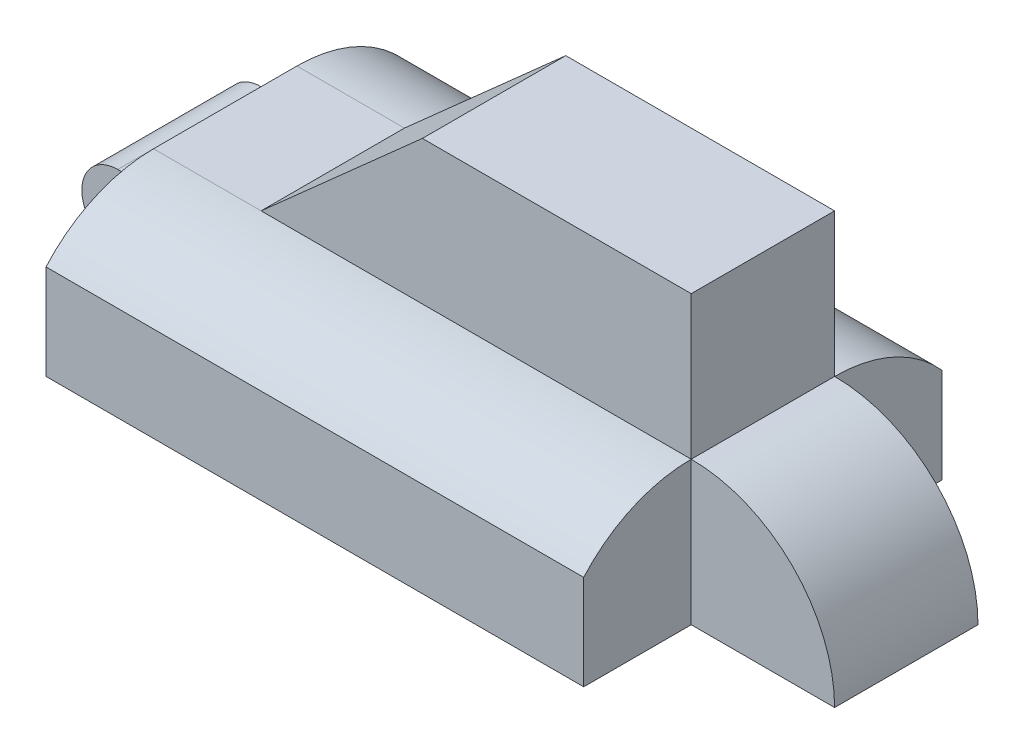
SolidWorks part; units mm, degrees
ref_plane "Front Plane" through (0, 0, 0) normal (0, 0, 1) x (1, 0, 0)
ref_plane "Top Plane" through (0, 0, 0) normal (0, 1, 0) x (1, 0, 0)
ref_plane "Right Plane" through (0, 0, 0) normal (1, 0, 0) x (0, 0, -1)
sketch "Sketch1" plane through (0, 0, 0) normal (0, 1, 0) x (1, 0, 0)
  line L1 (47.625, 31.75) -> (-47.625, 31.75)
  line L2 (47.625, 31.75) -> (47.625, -31.75)
  line L3 (47.625, -31.75) -> (-47.625, -31.75)
  line L4 (-47.625, 31.75) -> (-47.625, -31.75)
  line L5 (47.625, 31.75) -> (-47.625, -31.75) construction
  line L6 (47.625, -31.75) -> (-47.625, 31.75) construction
  point P0 (0, 0)
extrude "Boss-Extrude1" add sketch "Sketch1" along normal blind 25.4 contours L2 L3 L4 L1
sketch "Sketch2" plane through (0, 25.4, 0) normal (0, 1, 0) x (1, 0, 0)
  line L0 (47.625, 31.75) -> (-47.625, 31.75) construction
  line L1 (47.625, -12.7) -> (-28.575, -12.7)
  line L2 (47.625, -12.7) -> (47.625, 12.7)
  line L3 (47.625, 12.7) -> (-28.575, 12.7)
  line L4 (-28.575, -12.7) -> (-28.575, 12.7)
  line L5 (47.625, -12.7) -> (-28.575, 12.7) construction
  line L6 (47.625, 12.7) -> (-28.575, -12.7) construction
  line L7 (47.625, 31.75) -> (47.625, -31.75) construction
  point P0 (9.525, 0)
  dimension "D1" = 31.75
  dimension "D2" = 25.4
  dimension "D3" = 76.2
  dimension "D4" = 0
extrude "Boss-Extrude2" add sketch "Sketch2" along normal blind 25.4
sketch "Sketch3" plane through (0, 0, 12.7) normal (0, 0, 1) x (1, 0, 0)
  line L0 (-28.575, 25.4) -> (0, 50.8)
  line L1 (-28.575, 50.8) -> (47.625, 50.8) construction
  line L2 (0, 50.8) -> (-28.575, 25.4)
  line L3 (-28.575, 50.8) -> (-28.575, 25.4)
  line L4 (-28.575, 50.8) -> (0, 50.8)
  line M3 (47.625, 50.8) -> (-28.575, 50.8)
  line M4 (-28.575, 50.8) -> (-28.575, 25.4)
extrude "Cut-Extrude1" cut sketch "Sketch3" against normal blind 25.4 contours L0 M4 M3
sketch "Sketch4" plane through (47.625, 0, 0) normal (1, 0, 0) x (0, 0, -1)
  line L0 (31.75, 0) -> (-31.75, 0) construction
  line L1 (-12.7, 25.4) -> (12.7, 25.4)
  line L2 (-12.7, 25.4) -> (-12.7, 0)
  line L3 (-12.7, 0) -> (12.7, 0)
  line L4 (12.7, 25.4) -> (12.7, 0)
  dimension "D1" = 25.4
extrude "Boss-Extrude3" add sketch "Sketch4" along normal blind 25.4
sketch "Sketch5" plane through (0, 0, -12.7) normal (0, 0, -1) x (-1, 0, 0)
  line L0 (-73.025, 0) -> (-73.025, 25.4) construction
  line L1 (-73.025, 0) -> (-47.625, 0)
  line L2 (-47.625, 0) -> (-47.625, 25.4)
  line L3 (-73.025, 0) -> (-73.025, 25.4)
  line L4 (-73.025, 25.4) -> (-47.625, 25.4)
  arc A0 (-47.625, 25.4) -> (-73.025, 0) centre (-47.625, 0) ccw
  line M5 (-47.625, 25.4) -> (-73.025, 25.4)
  line M6 (-73.025, 25.4) -> (-73.025, 0)
extrude "Cut-Extrude2" cut sketch "Sketch5" against normal blind 25.4 contours A0 M5 M6
sketch "Sketch7" plane through (47.625, 0, 0) normal (1, 0, 0) x (0, 0, -1)
  line L0 (-31.75, 25.4) -> (-31.75, 0) construction
  line L1 (31.75, 25.4) -> (31.75, 0) construction
  line L2 (-31.75, 16.8005) -> (-31.75, 25.4)
  line L3 (-31.75, 25.4) -> (-12.7, 25.4)
  line L4 (12.7, 25.4) -> (31.75, 25.4)
  line L5 (31.75, 25.4) -> (31.75, 16.8005)
  arc A0 (-12.7, 25.4) -> (-31.75, 16.8005) centre (-12.7, 0) ccw
  arc A1 (12.7, 25.4) -> (31.75, 16.8005) centre (12.7, 0) cw
extrude "Cut-Extrude3" cut sketch "Sketch7" against normal blind 95.25 contours L3 A0 L2 | L5 A1 L4
sketch "." plane through (-47.625, 0, 0) normal (-1, 0, 0) x (0, 0, 1)
  line L1 (12.7, 6.35) -> (-12.7, 6.35)
  line L2 (12.7, 6.35) -> (12.7, 19.05)
  line L3 (12.7, 19.05) -> (-12.7, 19.05)
  line L4 (-12.7, 6.35) -> (-12.7, 19.05)
  line L6 (-12.7, 25.4) -> (12.7, 25.4) construction
  dimension "D1" = 25.4
  dimension "D2" = 12.7
  dimension "D3" = 6.35
extrude "Boss-Extrude4" add sketch "." along normal blind 12.7
sketch "Sketch9" plane through (0, 0, 12.7) normal (0, 0, 1) x (1, 0, 0)
  line L0 (-60.325, 6.35) -> (-60.325, 19.05) construction
  line L1 (-60.325, 19.05) -> (-47.625, 19.05) construction
  line L2 (-60.325, 12.7) -> (-60.325, 19.05)
  line L3 (-60.325, 19.05) -> (-47.625, 19.05)
  line L4 (-60.325, 12.7) -> (-60.325, 6.35)
  line L5 (-60.325, 6.35) -> (-47.625, 6.35)
  line L6 (-47.625, 6.35) -> (-60.325, 6.35)
  circle A0 centre (-53.975, 12.7) radius 6.35
  line M4 (-60.325, 19.05) -> (-60.325, 6.35)
  line M5 (-60.325, 6.35) -> (-47.625, 6.35)
  dimension "D2" = 12.7
  dimension "D3" = 6.35
  dimension "D1" = 6.35
extrude "Cut-Extrude4" cut sketch "Sketch9" against normal blind 25.4 contours A0 M4 M5 | A0 L3 M4
sketch "Sketch10" plane through (0, 0, 12.7) normal (0, 0, 1) x (1, 0, 0)
  circle A0 centre (-53.975, 12.7) radius 2.54
extrude "Cut-Extrude5" cut sketch "Sketch10" against normal blind 25.4 contours A0
scale "Scale1" scale about centroid uniform scaling yes scale factor 0.5
